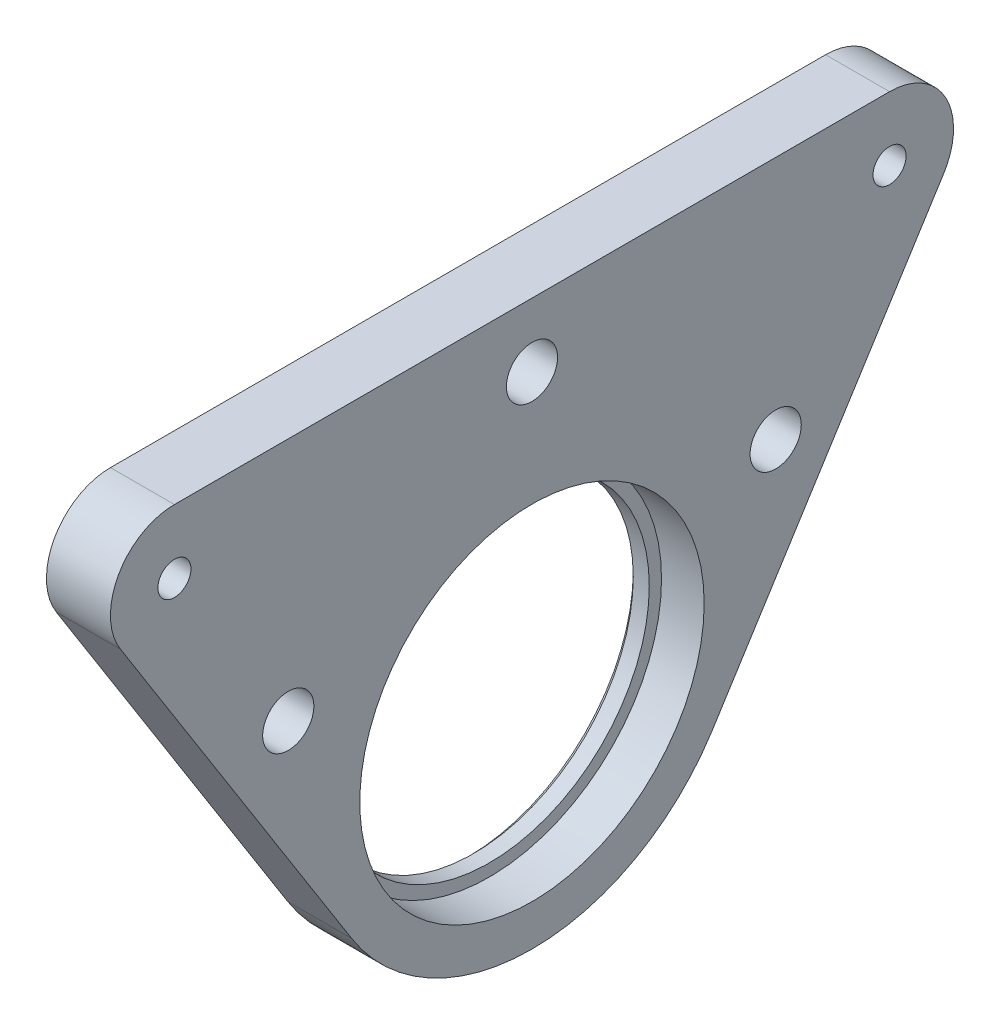
SolidWorks part; units mm, degrees
ref_plane "Front Plane" through (0, 0, 0) normal (0, 0, 1) x (1, 0, 0)
ref_plane "Top Plane" through (0, 0, 0) normal (0, 1, 0) x (1, 0, 0)
ref_plane "Right Plane" through (0, 0, 0) normal (1, 0, 0) x (0, 0, -1)
sketch "Sketch1" plane through (0, 0, 0) normal (1, 0, 0) x (0, 0, -1)
  circle A0 centre (0, 0) radius 15
  circle A1 centre (0, 0) radius 20
  dimension "D1" = 30
  dimension "D2" = 40
extrude "Boss-Extrude1" add sketch "Sketch1" along normal blind 2
sketch "Sketch2" plane through (2, 0, 0) normal (1, 0, 0) x (0, 0, -1)
  circle A0 centre (0, 0) radius 16
  circle A1 centre (0, 0) radius 20 construction
  circle A2 centre (0, 0) radius 20
  dimension "D1" = 32
extrude "Boss-Extrude2" add sketch "Sketch2" along normal blind 4
sketch "Sketch3" plane through (6, 0, 0) normal (1, 0, 0) x (0, 0, -1)
  line L0 (-33.5359, 26.8817) -> (0, 0) construction
  line L1 (0, 0) -> (33.5359, 26.8817) construction
  line L2 (-38.6088, 23.6778) -> (-16.9099, -10.6797)
  line L3 (-33.5359, 32.8817) -> (33.5359, 32.8817)
  line L4 (16.9099, -10.6797) -> (38.6088, 23.6778)
  circle A0 centre (-33.5359, 26.8817) radius 2
  circle A1 centre (33.5359, 26.8817) radius 2
  arc A2 (-33.5359, 32.8817) -> (-38.6088, 23.6778) centre (-33.5359, 26.8817) ccw
  arc A3 (38.6088, 23.6778) -> (33.5359, 32.8817) centre (33.5359, 26.8817) ccw
  circle A4 centre (0, 0) radius 20 construction
  arc A5 (16.9099, -10.6797) -> (-16.9099, -10.6797) centre (0, 0) ccw
  circle A6 centre (-33.5359, 26.8817) radius 6 construction
  circle A7 centre (33.5359, 26.8817) radius 6 construction
  dimension "D1" = 4
  dimension "D2" = 102.57
  dimension "D3" = 42.98
  dimension "D4" = 4
extrude "Boss-Extrude3" add sketch "Sketch3" against normal up to surface (6 mm away) up to face at (0, 0, -20)
sketch "Sketch4" plane through (6, 0, 0) normal (1, 0, 0) x (0, 0, -1)
  line L0 (-33.5359, 26.8817) -> (-22.8562, 9.9718) construction
  line L1 (-38.6088, 23.6778) -> (-16.9099, -10.6797) construction
  line L2 (0, 0) -> (0, 15) construction
  line L3 (33.5359, 26.8817) -> (22.8562, 9.9718) construction
  circle A0 centre (-22.8562, 9.9718) radius 2.4
  circle A2 centre (0, 0) radius 15 construction
  circle A3 centre (22.8562, 9.9718) radius 2.4
  circle A4 centre (0, 26.8817) radius 2.4
  dimension "D1" = 4.8
  dimension "D2" = 20
extrude "Cut-Extrude1" cut sketch "Sketch4" against normal up to surface (6 mm away) up to face at (0, 14.2393, 0)
sketch "Sketch5" plane through (0, 0, 0) normal (1, 0, 0) x (0, 0, -1)
  circle A0 centre (33.5359, 26.8817) radius 2 construction
  circle A1 centre (-33.5359, 26.8817) radius 2 construction
  circle A2 centre (33.5359, 26.8817) radius 2
  circle A3 centre (-33.5359, 26.8817) radius 2
  circle A4 centre (-33.5359, 26.8817) radius 1.55
  circle A5 centre (33.5359, 26.8817) radius 1.55
  dimension "D1" = 3.1
extrude "Boss-Extrude4" add sketch "Sketch5" along normal up to surface (6 mm away)
sketch "Sketch6" plane through (6, 0, 0) normal (1, 0, 0) x (0, 0, -1)
  circle A0 centre (0, 0) radius 16 construction
  circle A1 centre (0, 0) radius 16
  circle A2 centre (0, 0) radius 16.15
  dimension "D1" = 0.15
extrude "Cut-Extrude2" cut sketch "Sketch6" against normal up to surface (4 mm away) up to face at (2, 0, -15)
chamfer "Chamfer1" distance 0.5 angle 45 1 edges at (0, 0, -15)
